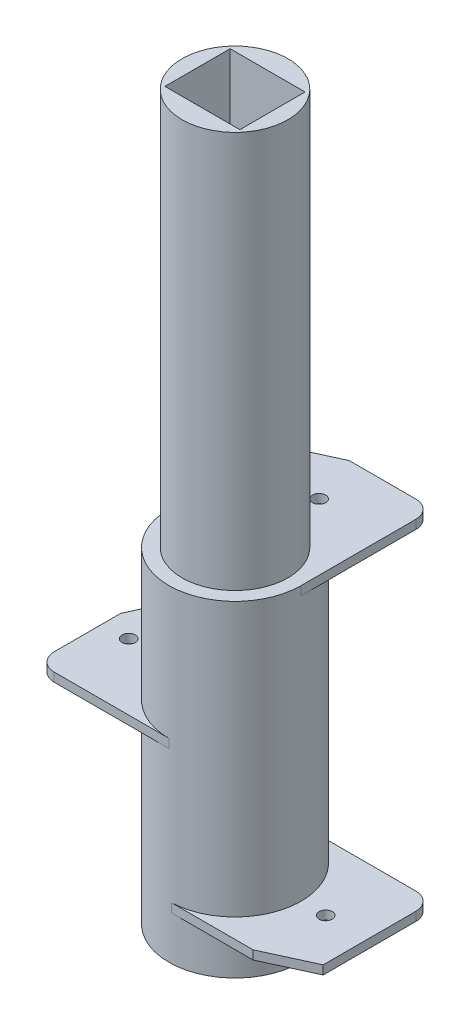
SolidWorks part; units mm, degrees
material "ABS"
ref_plane "Front Plane" through (0, 0, 0) normal (0, 0, 1) x (1, 0, 0)
ref_plane "Top Plane" through (0, 0, 0) normal (0, 1, 0) x (1, 0, 0)
ref_plane "Right Plane" through (0, 0, 0) normal (1, 0, 0) x (0, 0, -1)
sketch "Sketch1" plane through (0, 0, 0) normal (0, 1, 0) x (1, 0, 0)
  circle A0 centre (0, 0) radius 7.5
  dimension "D1" = 15
extrude "Boss-Extrude6" add sketch "Sketch1" along normal blind 5
sketch "Sketch16" plane through (0, 5, 0) normal (0, 1, 0) x (1, 0, 0)
  line L1 (0, 7.5) -> (15, 7.5)
  line L3 (0, -7.5) -> (15, -7.5)
  line L4 (15, 7.5) -> (15, -7.5)
  circle A0 centre (0, 0) radius 7.5 construction
  arc A1 (0, 7.5) -> (0.273, -7.5) centre (0, -0.0025) cw
  dimension "D1" = 15
extrude "Boss-Extrude7" add sketch "Sketch16" along normal blind 1 separate body contours L1 A1 L3 L4
sketch "Sketch22" plane through (0, 5, 0) normal (0, 1, 0) x (1, 0, 0)
  circle A0 centre (0, 0) radius 7.5
extrude "Boss-Extrude12" add sketch "Sketch22" along normal blind 8
sketch "Sketch30" plane through (0, 0, 0) normal (0, -1, 0) x (1, 0, 0)
  circle A0 centre (0, 0) radius 4.2
  dimension "D1" = 8.4
extrude "Cut-Extrude8" cut sketch "Sketch30" against normal blind 2
sketch "Sketch31" plane through (0, 2, 0) normal (0, -1, 0) x (1, 0, 0)
  circle A0 centre (0, 0) radius 2.1
  dimension "D1" = 4.2
extrude "Cut-Extrude9" cut sketch "Sketch31" against normal blind 9
sketch "Sketch33" plane through (0, 13, 0) normal (0, 1, 0) x (1, 0, 0)
  circle A0 centre (0, 0) radius 7.5
extrude "Boss-Extrude19" add sketch "Sketch33" along normal blind 8
sketch "Sketch34" plane through (0, 21, 0) normal (0, 1, 0) x (1, 0, 0)
  line L1 (0, 7.5) -> (-15, 7.5)
  line L3 (0, -7.5) -> (-15, -7.5)
  line L4 (-15, 7.5) -> (-15, -7.5)
  circle A0 centre (0, 0) radius 7.5 construction
  arc A1 (0, 7.5) -> (0, -7.5) centre (0, 0) ccw
  dimension "D1" = 15
extrude "Boss-Extrude20" add sketch "Sketch34" along normal blind 1 separate body
sketch "Sketch35" plane through (0, 21, 0) normal (0, 1, 0) x (1, 0, 0)
  circle A0 centre (0, 0) radius 7.5
extrude "Boss-Extrude21" add sketch "Sketch35" along normal blind 15
sketch "Sketch36" plane through (0, 36, 0) normal (0, 1, 0) x (1, 0, 0)
  line L6 (7.5, 0) -> (7.5, 15)
  line L7 (7.5, 15) -> (-7.5, 15)
  line L8 (-7.5, 0) -> (-7.5, 15)
  circle A1 centre (0, 0) radius 7.5 construction
  arc A2 (-7.5, 0) -> (7.5, 0) centre (0, 0) cw
extrude "Boss-Extrude22" add sketch "Sketch36" along normal blind 1 separate body
sketch "Sketch37" plane through (0, 36, 0) normal (0, 1, 0) x (1, 0, 0)
  circle A0 centre (0, 0) radius 7.5
extrude "Boss-Extrude23" add sketch "Sketch37" along normal blind 1
sketch "Sketch38" plane through (0, 37, 0) normal (0, 1, 0) x (1, 0, 0)
  circle A0 centre (0, 0) radius 6
  dimension "D1" = 12
extrude "Boss-Extrude24" add sketch "Sketch38" along normal blind 45
sketch "Sketch40" plane through (0, 37, 0) normal (0, 1, 0) x (1, 0, 0)
  line L0 (-7.5, 12.5) -> (-2.0456, 15)
  line L1 (-7.5, 15) -> (-7.5, 0) construction
  line L3 (7.5, 0) -> (7.5, 15) construction
  line L4 (-7.5, 12.5) -> (-7.5, 15)
  line L5 (-7.5, 15) -> (7.5, 15)
  line L6 (7.5, 15) -> (7.5, 14.4863)
  line L7 (-2.0456, 15) -> (-7.5, 15)
  line M5 (7.5, 15) -> (-7.5, 15)
  line M6 (-7.5, 15) -> (-7.5, 0)
  dimension "D1" = 6
  dimension "D2" = 2.5
extrude "Cut-Extrude11" cut sketch "Sketch40" against normal blind 1 contours L0 M6 M5
sketch "Sketch41" plane through (0, 6, 0) normal (0, 1, 0) x (1, 0, 0)
  line L0 (15, -5) -> (9.5456, -7.5)
  line L1 (15, 7.5) -> (15, -7.5) construction
  line L2 (0.273, -7.5) -> (15, -7.5) construction
  line L3 (15, -5) -> (15, -7.5)
  line L4 (15, -7.5) -> (9.5456, -7.5)
  dimension "D1" = 2.5
  dimension "D2" = 6
extrude "Cut-Extrude12" cut sketch "Sketch41" against normal blind 1
sketch "Sketch42" plane through (0, 22, 0) normal (0, 1, 0) x (1, 0, 0)
  line L0 (-15, 2.0456) -> (-12.5, 7.5)
  line L1 (-15, 7.5) -> (-15, -7.5) construction
  line L2 (0, 7.5) -> (-15, 7.5) construction
  line L3 (-15, 2.0456) -> (-15, 7.5)
  line L4 (-15, 7.5) -> (-12.5, 7.5)
  dimension "D1" = 2.5
  dimension "D2" = 6
extrude "Cut-Extrude13" cut sketch "Sketch42" against normal blind 1
sketch "Sketch44" plane through (0, 82, 0) normal (0, 1, 0) x (1, 0, 0)
  line L1 (-4.25, 3.7) -> (4.25, 3.7)
  line L2 (-4.25, 3.7) -> (-4.25, -3.7)
  line L3 (-4.25, -3.7) -> (4.25, -3.7)
  line L4 (4.25, 3.7) -> (4.25, -3.7)
  line L5 (-4.25, 3.7) -> (4.25, -3.7) construction
  line L6 (-4.25, -3.7) -> (4.25, 3.7) construction
  point P0 (0, 0)
  dimension "D1" = 7.4
  dimension "D2" = 8.5
extrude "Cut-Extrude19" cut sketch "Sketch44" against normal blind 20
fillet "Fillet3" radius 2 1 edges at (15, 5.5, -7.5)
fillet "Fillet4" radius 2 1 edges at (-15, 21.5, 7.5)
fillet "Fillet5" radius 2 1 edges at (7.5, 36.5, -15)
sketch "Sketch51" plane through (0, 5, 0) normal (0, -1, 0) x (1, 0, 0)
  line L1 (0, -7.5) -> (13, -7.5) construction
  line L2 (15, -5.5) -> (15, 5) construction
  circle A0 centre (11, -4) radius 0.7
  dimension "D1" = 1.4
  dimension "D2" = 3.5
  dimension "D3" = 4
extrude "Boss-Extrude25" add sketch "Sketch51" along normal blind 1.2
sketch "Sketch52" plane through (0, 21, 0) normal (0, -1, 0) x (1, 0, 0)
  line L0 (-15, -2.0456) -> (-15, 5.5) construction
  line L1 (-13, 7.5) -> (0, 7.5) construction
  circle A0 centre (-11, 4) radius 0.7
  dimension "D1" = 1.4
  dimension "D2" = 4
  dimension "D3" = 3.5
sketch "Sketch53" plane through (0, 36, 0) normal (0, -1, 0) x (1, 0, 0)
  line L2 (-7.5, -12.5) -> (-7.5, 0) construction
  line L3 (5.5, -15) -> (-2.0456, -15) construction
  circle A1 centre (-3.5, -11.5) radius 0.7
  dimension "D1" = 1.4
  dimension "D2" = 4
  dimension "D3" = 3.5
extrude "Boss-Extrude27" add sketch "Sketch53" along normal blind 1.2
extrude "Boss-Extrude28" add sketch "Sketch52" along normal blind 1.2 contours A0
sketch "Sketch58" plane through (0, 21, 0) normal (0, -1, 0) x (1, 0, 0)
  circle A0 centre (-12.0542, 0) radius 0.75
  dimension "D1" = 1.5
sketch "Sketch59" plane through (0, 36, 0) normal (0, -1, 0) x (1, 0, 0)
  circle A0 centre (0, -9.536) radius 0.75
  dimension "D1" = 1.5
extrude "Cut-Extrude23" cut sketch "Sketch59" against normal blind 2 contours A0
sketch "Sketch60" plane through (0, 5, 0) normal (0, -1, 0) x (1, 0, 0)
  circle A0 centre (10.2862, 0) radius 0.75
  dimension "D1" = 1.5
extrude "Cut-Extrude25" cut sketch "Sketch60" against normal blind 2 contours A0
extrude "Cut-Extrude29" cut sketch "Sketch58" against normal blind 10 contours A0
